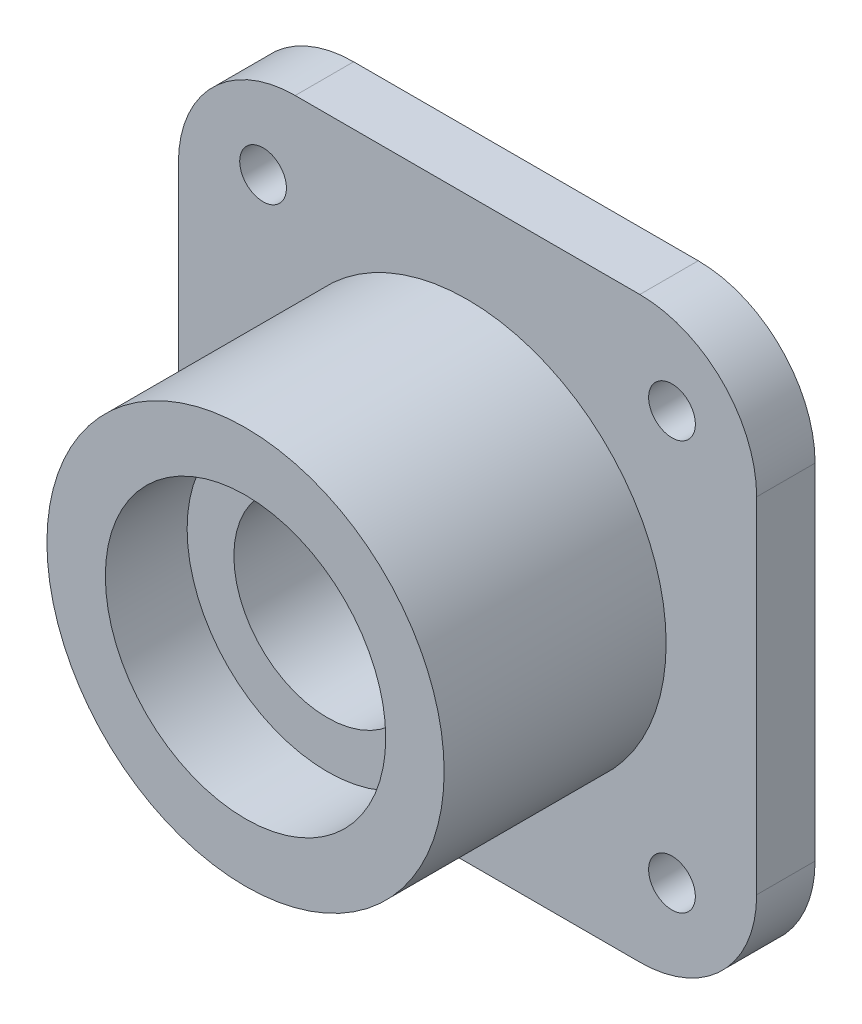
SolidWorks part; units mm, degrees
ref_plane "Front Plane" through (0, 0, 0) normal (0, 0, 1) x (1, 0, 0)
ref_plane "Top Plane" through (0, 0, 0) normal (0, 1, 0) x (1, 0, 0)
ref_plane "Right Plane" through (0, 0, 0) normal (1, 0, 0) x (0, 0, -1)
sketch "Sketch3" plane through (0, 0, 0) normal (1, 0, 0) x (0, 0, -1)
  line L0 (0, 0) -> (64.3605, 0) construction
  line L1 (0, 12) -> (7, 12)
  line L2 (7, 12) -> (7, 8)
  line L3 (7, 8) -> (17, 8)
  line L4 (17, 8) -> (17, 12)
  line L5 (17, 12) -> (24, 12)
  line L6 (24, 12) -> (24, 35)
  line L7 (24, 35) -> (19, 35)
  line L8 (19, 35) -> (19, 17)
  line L9 (19, 17) -> (0, 17)
  line L10 (0, 17) -> (0, 12)
  point P5 (0, 0)
  dimension "D1" = 12
  dimension "D2" = 8
  dimension "D3" = 5
  dimension "D4" = 10
  dimension "D5" = 7
  dimension "D6" = 5
  dimension "D7" = 35
revolve "Revolve1" add sketch "Sketch3" angle 360 about L0
sketch "Sketch4" plane through (0, 0, -19) normal (0, 0, 1) x (1, 0, 0)
  line L0 (-24.7487, 24.7487) -> (24.7487, 24.7487)
  line L1 (-24.7487, 24.7487) -> (-24.7487, -24.7487)
  line L2 (24.7487, 24.7487) -> (24.7487, -24.7487)
  line L3 (-24.7487, -24.7487) -> (24.7487, -24.7487)
  circle A0 centre (0, 0) radius 35 construction
  circle A1 centre (0, 0) radius 35
  point P6 (-24.7487, 0)
  point P8 (0, 24.7487)
  circle M6 centre (0, 0) radius 35
extrude "Cut-Extrude1" cut sketch "Sketch4" against normal blind 10 contours L2 M6 | L0 M6 | L1 M6 | L3 M6
fillet "Fillet1" radius 10 4 edges at (24.7487, 24.7487, -21.5) (24.7487, -24.7487, -21.5) (-24.7487, -24.7487, -21.5) (-24.7487, 24.7487, -21.5)
sketch "Sketch5" plane through (0, 0, -24) normal (0, 0, -1) x (-1, 0, 0)
  line L1 (-17.5, -17.5) -> (17.5, -17.5) construction
  line L2 (-17.5, -17.5) -> (-17.5, 17.5) construction
  line L3 (-17.5, 17.5) -> (17.5, 17.5) construction
  line L4 (17.5, -17.5) -> (17.5, 17.5) construction
  line L5 (-17.5, -17.5) -> (17.5, 17.5) construction
  line L6 (-17.5, 17.5) -> (17.5, -17.5) construction
  circle A0 centre (-17.5, 17.5) radius 2
  circle A1 centre (17.5, 17.5) radius 2
  circle A2 centre (17.5, -17.5) radius 2
  circle A3 centre (-17.5, -17.5) radius 2
  point P0 (0, 0)
  dimension "D2" = 4
  dimension "D1" = 35
extrude "Cut-Extrude2" cut sketch "Sketch5" against normal blind 10
